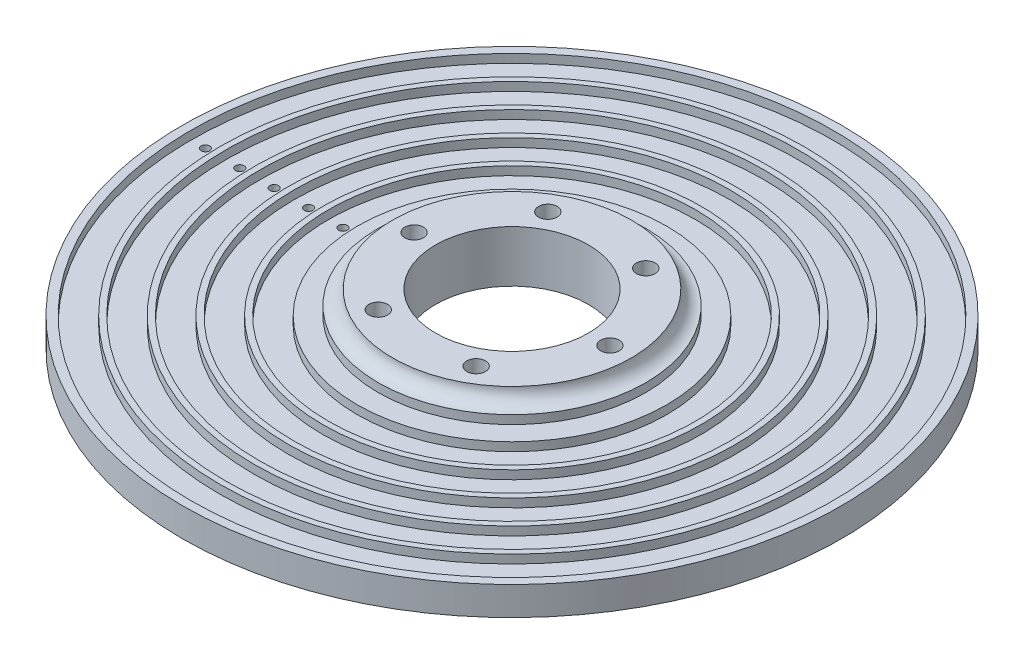
SolidWorks part; units mm, degrees
ref_plane "Front Plane" through (0, 0, 0) normal (0, 0, 1) x (1, 0, 0)
ref_plane "Top Plane" through (0, 0, 0) normal (0, 1, 0) x (1, 0, 0)
ref_plane "Right Plane" through (0, 0, 0) normal (1, 0, 0) x (0, 0, -1)
sketch "Sketch1" plane through (0, 0, 0) normal (0, 1, 0) x (1, 0, 0)
  circle A0 centre (0, 0) radius 13.335
  circle A1 centre (0, 0) radius 23.335
  dimension "D1" = 26.67
  dimension "D2" = 10
extrude "Boss-Extrude1" add sketch "Sketch1" along normal blind 4
sketch "Sketch3" plane through (0, 0, 0) normal (0, -1, 0) x (1, 0, 0)
  circle A0 centre (0, 0) radius 13.335
  circle A1 centre (0, 0) radius 57.5
  circle A3 centre (0, 0) radius 13.335 construction
  dimension "D1" = 115
extrude "Boss-Extrude2" add sketch "Sketch3" along normal blind 5
sketch "Sketch4" plane through (0, 0, 0) normal (0, 1, 0) x (1, 0, 0)
  line L1 (27, 0) -> (32, 0) construction
  line L2 (32, 0) -> (33, 0) construction
  line L3 (33, 0) -> (38, 0) construction
  line L4 (38, 0) -> (39, 0) construction
  line L5 (39, 0) -> (44, 0) construction
  line L6 (44, 0) -> (45, 0) construction
  line L7 (45, 0) -> (50, 0) construction
  line L8 (50, 0) -> (51, 0) construction
  line L9 (51, 0) -> (56, 0) construction
  circle A0 centre (0, 0) radius 27
  circle A1 centre (0, 0) radius 32
  circle A2 centre (0, 0) radius 33
  circle A3 centre (0, 0) radius 38
  circle A5 centre (0, 0) radius 39
  circle A6 centre (0, 0) radius 44
  circle A8 centre (0, 0) radius 45
  circle A9 centre (0, 0) radius 50
  circle A10 centre (0, 0) radius 51
  circle A11 centre (0, 0) radius 56
  dimension "D1" = 1
  dimension "D2" = 5
  dimension "D3" = 54
extrude "Cut-Extrude2" cut sketch "Sketch4" against normal blind 1.5 contours A1 A0 | A3 A2 | A6 A5 | A9 A8 | A11 A10
sketch "Sketch5" plane through (0, 0, 0) normal (0, 0, 1) x (1, 0, 0)
  circle A0 centre (-23.335, 4) radius 2.5
  dimension "D1" = 5
ref_axis "Axis1" through (0, 4, 0) along (0, -1, 0)
revolve "Cut-Revolve1" cut sketch "Sketch5" angle 360 about axis through (0, 4, 0) along (0, -1, 0)
sketch "Sketch2" plane through (0, 4, 0) normal (0, 1, 0) x (1, 0, 0)
  line L0 (-13.335, 0) -> (-20.835, 0) construction
  line L1 (17.085, 0) -> (8.5425, 14.796) construction
  line L2 (8.5425, 14.796) -> (-8.5425, 14.796) construction
  line L3 (-8.5425, 14.796) -> (-17.085, 0) construction
  line L4 (-17.085, 0) -> (-8.5425, -14.796) construction
  line L5 (-8.5425, -14.796) -> (8.5425, -14.796) construction
  line L6 (8.5425, -14.796) -> (17.085, 0) construction
  circle A0 centre (0, 0) radius 14.796 construction
  circle A1 centre (-8.5425, 14.796) radius 1.625
  circle A2 centre (-17.085, 0) radius 1.625
  circle A3 centre (-8.5425, -14.796) radius 1.625
  circle A4 centre (8.5425, -14.796) radius 1.625
  circle A5 centre (17.085, 0) radius 1.625
  circle A6 centre (8.5425, 14.796) radius 1.625
  circle A7 centre (0, 0) radius 13.335 construction
  circle A8 centre (0, 0) radius 20.835 construction
  dimension "D2" = 3.25
extrude "Cut-Extrude1" cut sketch "Sketch2" against normal through all
sketch "Sketch6" plane through (0, -1.5, 0) normal (0, 1, 0) x (1, 0, 0)
  line L0 (-56, 0) -> (-51, 0) construction
  line L1 (-50, 0) -> (-45, 0) construction
  line L2 (-44, 0) -> (-39, 0) construction
  line L3 (-38, 0) -> (-33, 0) construction
  line L4 (-32, 0) -> (-27, 0) construction
  circle A0 centre (0, 0) radius 56 construction
  circle A1 centre (0, 0) radius 56 construction
  circle A2 centre (0, 0) radius 51 construction
  circle A3 centre (0, 0) radius 50 construction
  circle A4 centre (0, 0) radius 45 construction
  circle A5 centre (0, 0) radius 44 construction
  circle A6 centre (0, 0) radius 39 construction
  circle A7 centre (0, 0) radius 38 construction
  circle A8 centre (0, 0) radius 38 construction
  circle A9 centre (0, 0) radius 33 construction
  circle A10 centre (0, 0) radius 32 construction
  circle A11 centre (0, 0) radius 32 construction
  circle A12 centre (0, 0) radius 27 construction
  circle A13 centre (-53.5, 0) radius 0.75
  circle A14 centre (-47.5, 0) radius 0.75
  circle A15 centre (-41.5, 0) radius 0.75
  circle A16 centre (-35.5, 0) radius 0.75
  circle A17 centre (-29.5, 0) radius 0.75
  dimension "D1" = 1.5
extrude "Cut-Extrude3" cut sketch "Sketch6" against normal through all
sketch "Sketch7" plane through (0, -5, 0) normal (0, -1, 0) x (1, 0, 0)
  circle A1 centre (-17.085, 0) radius 3
  circle A3 centre (8.5425, -14.796) radius 3
  circle A5 centre (8.5425, 14.796) radius 3
  dimension "D1" = 6
extrude "Cut-Extrude4" cut sketch "Sketch7" against normal blind 3
equation "\"1.5.00mm\"=5"
